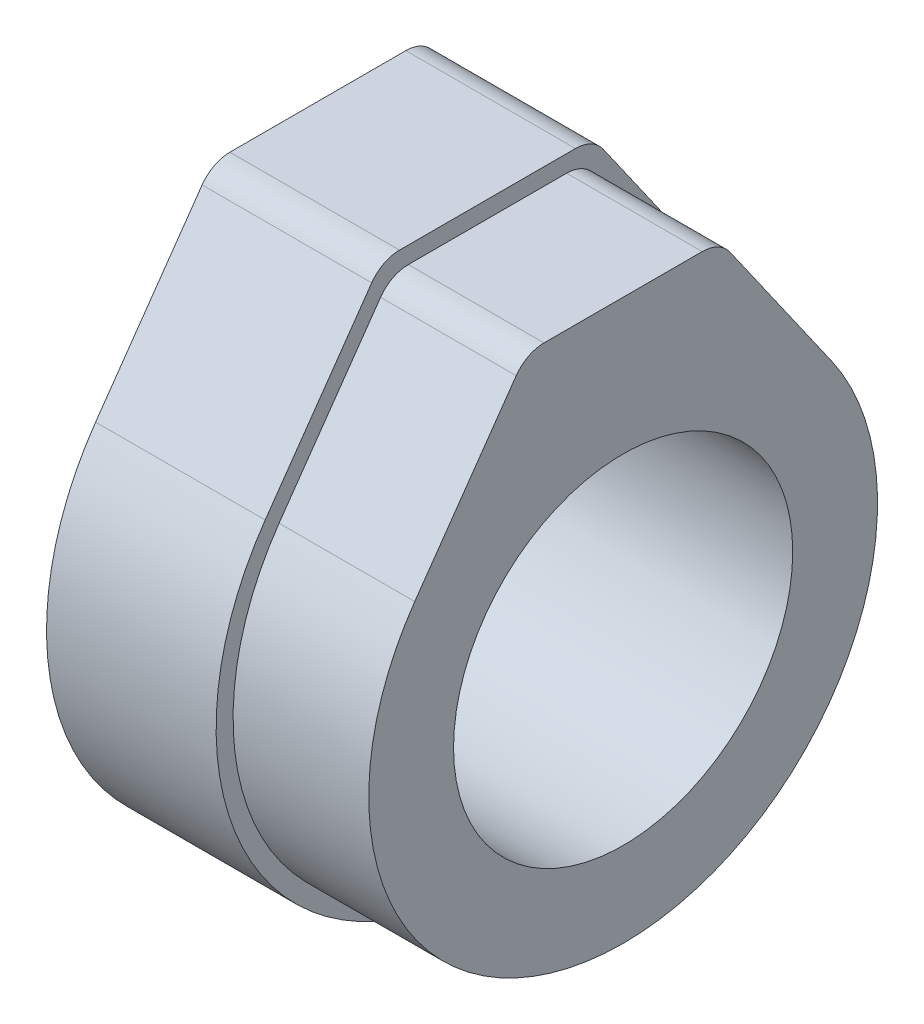
SolidWorks part; units mm, degrees
ref_plane "Ebene vorne" through (0, 0, 0) normal (0, 0, 1) x (1, 0, 0)
ref_plane "Ebene oben" through (0, 0, 0) normal (0, 1, 0) x (1, 0, 0)
ref_plane "Ebene rechts" through (0, 0, 0) normal (1, 0, 0) x (0, 0, -1)
sketch "Skizze1" plane through (0, 0, 0) normal (1, 0, 0) x (0, 0, -1)
  line L0 (-13.1064, 9.1772) -> (-6.2285, 19)
  line L1 (-6.2285, 19) -> (6.2285, 19)
  line L2 (6.2285, 19) -> (13.1064, 9.1772)
  line L3 (0, 0) -> (0, 19) construction
  circle A0 centre (0, 0) radius 16
  dimension "D2" = 32
  dimension "D1" = 70
  dimension "D3" = 19
extrude "Aufsatz-Linear austragen1" add sketch "Skizze1" along normal blind 10
sketch "Skizze2" plane through (10, 0, 0) normal (1, 0, 0) x (0, 0, -1)
  line L0 (-6.2285, 19) -> (6.2285, 19) construction
  line L1 (6.2285, 19) -> (13.1064, 9.1772) construction
  line L2 (-13.1064, 9.1772) -> (-6.2285, 19) construction
  line L3 (-6.2285, 19) -> (6.2285, 19)
  line L4 (6.2285, 19) -> (13.1064, 9.1772)
  line L5 (-13.1064, 9.1772) -> (-6.2285, 19)
  line L6 (-12.2873, 8.6036) -> (-5.7079, 18)
  line L7 (-5.7079, 18) -> (5.7079, 18)
  line L8 (5.7079, 18) -> (12.2873, 8.6036)
  arc A0 (-13.1064, 9.1772) -> (13.1064, 9.1772) centre (0, 0) ccw construction
  arc A1 (-13.1064, 9.1772) -> (13.1064, 9.1772) centre (0, 0) ccw
  arc A2 (-12.2873, 8.6036) -> (12.2873, 8.6036) centre (0, 0) ccw
  dimension "D1" = 1
extrude "Aufsatz-Linear austragen2" add sketch "Skizze2" along normal blind 8 contours L6 L7 L8 A2
fillet "Verrundung1" radius 2 4 edges at (14, 18, 5.7079) (14, 18, -5.7079) (5, 19, -6.2285) (5, 19, 6.2285)
sketch "Skizze3" plane through (18, 0, 0) normal (1, 0, 0) x (0, 0, -1)
  circle A0 centre (0, 0) radius 10
  dimension "D1" = 20
extrude "Schnitt-Linear austragen1" cut sketch "Skizze3" against normal up to next
